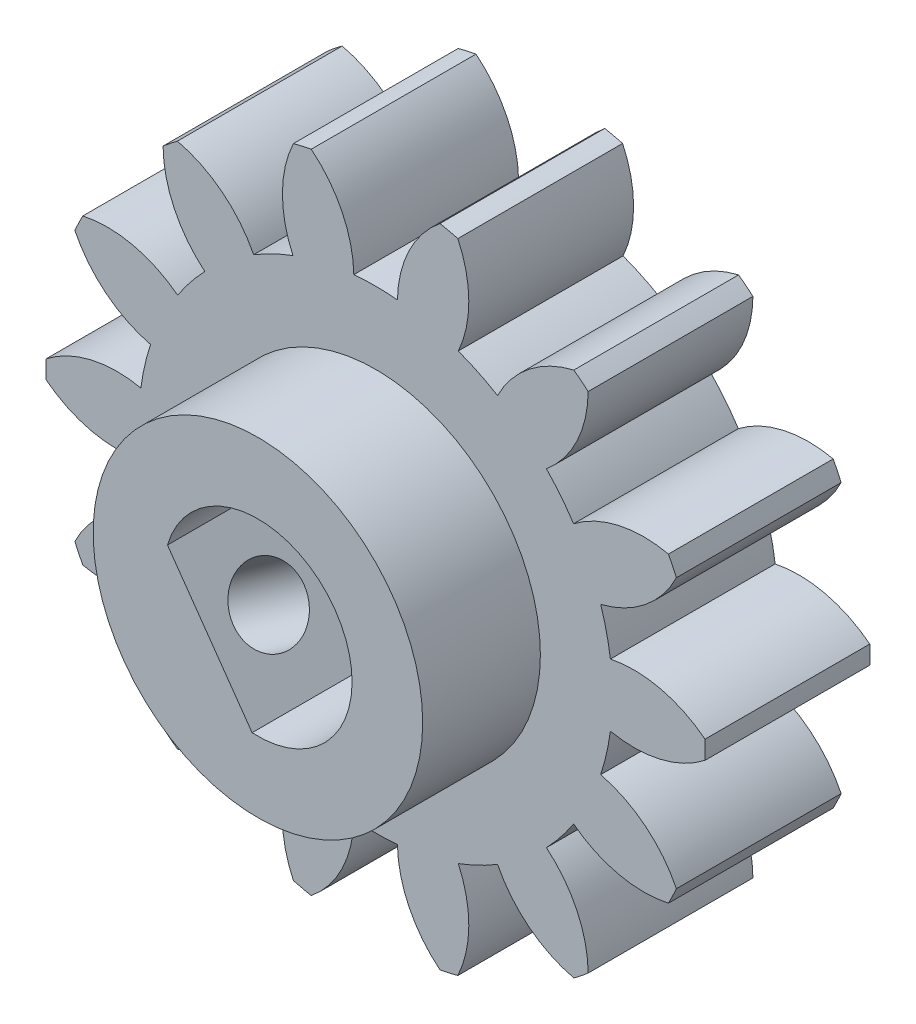
SolidWorks part; units mm, degrees
ref_plane "Front Plane" through (0, 0, 0) normal (0, 0, 1) x (1, 0, 0)
ref_plane "Top Plane" through (0, 0, 0) normal (0, 1, 0) x (1, 0, 0)
ref_plane "Right Plane" through (0, 0, 0) normal (1, 0, 0) x (0, 0, -1)
sketch "Sketch1" plane through (0, 0, 0) normal (0, 0, 1) x (1, 0, 0)
  arc A0 (-12.4397, -6.4229) -> (-8.4105, -5.5224) centre (-11.3944, -1.6357) ccw
  arc A1 (-8.4105, -5.5224) -> (-7.2555, -6.9708) centre (0, 0) ccw
  arc A2 (-7.2555, -6.9708) -> (-9.03, -10.6986) centre (-4.1302, -10.7448) ccw
  arc A3 (-9.03, -10.6986) -> (-8.421, -11.1842) centre (0, 0) ccw
  arc A4 (-8.421, -11.1842) -> (-5.1815, -8.6247) centre (-9.5563, -6.4176) ccw
  arc A5 (-5.1815, -8.6247) -> (-3.5124, -9.4285) centre (0, 0) ccw
  arc A6 (-3.5124, -9.4285) -> (-3.4938, -13.557) centre (0.9408, -11.4727) ccw
  arc A7 (-3.4938, -13.557) -> (-2.7344, -13.7304) centre (0, 0) ccw
  arc A8 (-2.7344, -13.7304) -> (-0.9263, -10.0188) centre (-5.8254, -9.9284) ccw
  arc A9 (-0.9263, -10.0188) -> (0.9263, -10.0188) centre (0, 0) ccw
  arc A10 (0.9263, -10.0188) -> (2.7344, -13.7304) centre (5.8254, -9.9284) ccw
  arc A11 (2.7344, -13.7304) -> (3.4938, -13.557) centre (0, 0) ccw
  arc A12 (3.4938, -13.557) -> (3.5124, -9.4285) centre (-0.9408, -11.4727) ccw
  arc A13 (3.5124, -9.4285) -> (5.1815, -8.6247) centre (0, 0) ccw
  arc A14 (5.1815, -8.6247) -> (8.421, -11.1842) centre (9.5563, -6.4176) ccw
  arc A15 (8.421, -11.1842) -> (9.03, -10.6986) centre (0, 0) ccw
  arc A16 (9.03, -10.6986) -> (7.2555, -6.9708) centre (4.1302, -10.7448) ccw
  arc A17 (7.2555, -6.9708) -> (8.4105, -5.5224) centre (0, 0) ccw
  arc A18 (8.4105, -5.5224) -> (12.4397, -6.4229) centre (11.3944, -1.6357) ccw
  arc A19 (12.4397, -6.4229) -> (12.7777, -5.7211) centre (0, 0) ccw
  arc A20 (12.7777, -5.7211) -> (9.5615, -3.1324) centre (8.3832, -7.8887) ccw
  arc A21 (9.5615, -3.1324) -> (9.9737, -1.3263) centre (0, 0) ccw
  arc A22 (9.9737, -1.3263) -> (13.9946, -0.3895) centre (10.9757, 3.4701) ccw
  arc A23 (13.9946, -0.3895) -> (13.9946, 0.3895) centre (0, 0) ccw
  arc A24 (13.9946, 0.3895) -> (9.9737, 1.3263) centre (10.9757, -3.4701) ccw
  arc A25 (9.9737, 1.3263) -> (9.5615, 3.1324) centre (0, 0) ccw
  arc A26 (9.5615, 3.1324) -> (12.7777, 5.7211) centre (8.3832, 7.8887) ccw
  arc A27 (12.7777, 5.7211) -> (12.4397, 6.4229) centre (0, 0) ccw
  arc A28 (12.4397, 6.4229) -> (8.4105, 5.5224) centre (11.3944, 1.6357) ccw
  arc A29 (8.4105, 5.5224) -> (7.2555, 6.9708) centre (0, 0) ccw
  arc A30 (7.2555, 6.9708) -> (9.03, 10.6986) centre (4.1302, 10.7448) ccw
  arc A31 (9.03, 10.6986) -> (8.421, 11.1842) centre (0, 0) ccw
  arc A32 (8.421, 11.1842) -> (5.1815, 8.6247) centre (9.5563, 6.4176) ccw
  arc A33 (5.1815, 8.6247) -> (3.5124, 9.4285) centre (0, 0) ccw
  arc A34 (3.5124, 9.4285) -> (3.4938, 13.557) centre (-0.9408, 11.4727) ccw
  arc A35 (3.4938, 13.557) -> (2.7344, 13.7304) centre (0, 0) ccw
  arc A36 (2.7344, 13.7304) -> (0.9263, 10.0188) centre (5.8254, 9.9284) ccw
  arc A37 (0.9263, 10.0188) -> (-0.9263, 10.0188) centre (0, 0) ccw
  arc A38 (-0.9263, 10.0188) -> (-2.7344, 13.7304) centre (-5.8254, 9.9284) ccw
  arc A39 (-2.7344, 13.7304) -> (-3.4938, 13.557) centre (0, 0) ccw
  arc A40 (-3.4938, 13.557) -> (-3.5124, 9.4285) centre (0.9408, 11.4727) ccw
  arc A41 (-3.5124, 9.4285) -> (-5.1815, 8.6247) centre (0, 0) ccw
  arc A42 (-5.1815, 8.6247) -> (-8.421, 11.1842) centre (-9.5563, 6.4176) ccw
  arc A43 (-8.421, 11.1842) -> (-9.03, 10.6986) centre (0, 0) ccw
  arc A44 (-9.03, 10.6986) -> (-7.2555, 6.9708) centre (-4.1302, 10.7448) ccw
  arc A45 (-7.2555, 6.9708) -> (-8.4105, 5.5224) centre (0, 0) ccw
  arc A46 (-8.4105, 5.5224) -> (-12.4397, 6.4229) centre (-11.3944, 1.6357) ccw
  arc A47 (-12.4397, 6.4229) -> (-12.7777, 5.7211) centre (0, 0) ccw
  arc A48 (-12.7777, 5.7211) -> (-9.5615, 3.1324) centre (-8.3832, 7.8887) ccw
  arc A49 (-9.5615, 3.1324) -> (-9.9737, 1.3263) centre (0, 0) ccw
  arc A50 (-9.9737, 1.3263) -> (-13.9946, 0.3895) centre (-10.9757, -3.4701) ccw
  arc A51 (-13.9946, 0.3895) -> (-13.9946, -0.3895) centre (0, 0) ccw
  arc A52 (-13.9946, -0.3895) -> (-9.9737, -1.3263) centre (-10.9757, 3.4701) ccw
  arc A53 (-9.9737, -1.3263) -> (-9.5615, -3.1324) centre (0, 0) ccw
  arc A54 (-9.5615, -3.1324) -> (-12.7777, -5.7211) centre (-8.3832, -7.8887) ccw
  arc A55 (-12.7777, -5.7211) -> (-12.4397, -6.4229) centre (0, 0) ccw
extrude "Boss-Extrude1" add sketch "Sketch1" along normal blind 7
sketch "Sketch2" plane through (0, 0, 7) normal (0, 0, 1) x (1, 0, 0)
  circle A0 centre (0, 0) radius 4
  circle A1 centre (0, 0) radius 7
  arc A2 (5.1815, 8.6247) -> (3.5124, 9.4285) centre (0, 0) ccw construction
  dimension "D1" = 14
  dimension "D2" = 8
extrude "Boss-Extrude2" add sketch "Sketch2" along normal blind 5
sketch "Sketch3" plane through (0, 0, 7) normal (0, 0, 1) x (1, 0, 0)
  circle A0 centre (0, 0) radius 4 construction
  circle A1 centre (0, 0) radius 4
extrude "Cut-Extrude1" cut sketch "Sketch3" against normal blind 15
sketch "Sketch4" plane through (0, 0, 0) normal (0, 0, -1) x (-1, 0, 0)
  line L0 (3.8418, 1.1139) -> (0.2465, -3.9924)
  line L1 (3.8418, 1.1139) -> (0.2465, -3.9924) construction
  arc A0 (0.2465, -3.9924) -> (3.8418, 1.1139) centre (0, 0) ccw
  circle A1 centre (0, 0) radius 4 construction
extrude "Boss-Extrude3" add sketch "Sketch4" against normal blind 12
ref_plane "Plane1" through (-10.2207, -7.1963, 0) normal (0.8177, 0.5757, 0) x (0, 0, -1)
sketch "Sketch5" plane through (-10.2207, -7.1963, 0) normal (0.8177, 0.5757, 0) x (0, 0, -1)
  line L0 (0, 3.1225) -> (0, -3.1225) construction
  line L1 (-12, 7) -> (-12, -7) construction
  circle A0 centre (-9.5, 0) radius 1.5
  point P5 (0, 0)
  dimension "D2" = 3
  dimension "D1" = 2.5
extrude "Cut-Extrude2" cut sketch "Sketch5" along normal blind 12
